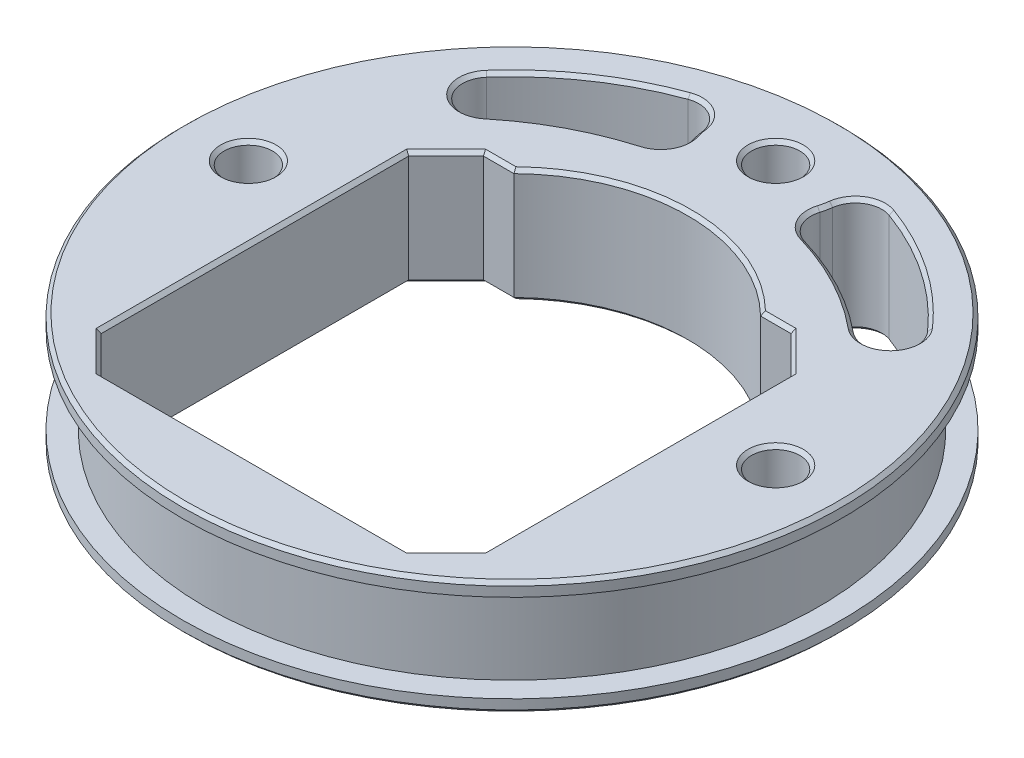
SolidWorks part; units mm, degrees
ref_plane "Front Plane" through (0, 0, 0) normal (0, 0, 1) x (1, 0, 0)
ref_plane "Top Plane" through (0, 0, 0) normal (0, 1, 0) x (1, 0, 0)
ref_plane "Right Plane" through (0, 0, 0) normal (1, 0, 0) x (0, 0, -1)
sketch "Sketch1" plane through (0, 0, 0) normal (0, 1, 0) x (1, 0, 0)
  line L0 (0, 0) -> (0, -7.5) construction
  line L1 (-17.4944, 14.25) -> (-14.0334, 14.25)
  line L2 (17.4944, 14.25) -> (21.75, 9.9944)
  line L3 (21.75, 9.9944) -> (21.75, -24.9944)
  line L4 (21.75, -24.9944) -> (17.4944, -29.25)
  line L5 (17.4944, -29.25) -> (-17.4944, -29.25)
  line L6 (-17.4944, -29.25) -> (-21.75, -24.9944)
  line L7 (-21.75, -24.9944) -> (-21.75, 9.9944)
  line L8 (-21.75, 9.9944) -> (-17.4944, 14.25)
  line L9 (14.0334, 14.25) -> (17.4944, 14.25)
  circle A0 centre (0, 0) radius 35 construction
  circle A1 centre (0, -7.5) radius 27.9127 construction
  circle A2 centre (0, 0) radius 30 construction
  circle A3 centre (0, 30) radius 2.75
  circle A4 centre (30, 0) radius 2.75
  circle A5 centre (-30, 0) radius 2.75
  circle A6 centre (0, 0) radius 37.5
  arc A7 (-20.9311, 17.8995) -> (20.9311, 17.8995) centre (0, -7.5) ccw construction
  arc A8 (7.1823, 27.8402) -> (7.4393, 29.0476) centre (0, 30) ccw
  arc A9 (6.9711, 32.7667) -> (-6.9711, 32.7667) centre (0, 0) ccw construction
  arc A10 (-25.0854, 22.203) -> (-20.9311, 17.8995) centre (-22.8389, 20.2147) ccw
  arc A11 (20.9311, 17.8995) -> (25.0854, 22.203) centre (22.8389, 20.2147) ccw
  arc A12 (-5.5389, 24.9433) -> (5.5389, 24.9433) centre (0, 30) ccw construction
  arc A13 (5.5389, 24.9433) -> (-5.5389, 24.9433) centre (0, -7.5) ccw construction
  arc A14 (-9.2152, 24.0963) -> (-20.9311, 17.8995) centre (0, -7.5) ccw
  arc A15 (20.9311, 17.8995) -> (9.2152, 24.0963) centre (0, -7.5) ccw
  arc A16 (25.0854, 22.203) -> (11.4394, 31.4863) centre (0, 0) ccw
  arc A17 (-11.4394, 31.4863) -> (-25.0854, 22.203) centre (0, 0) ccw
  arc A18 (-25.0854, 22.203) -> (25.0854, 22.203) centre (0, 0) ccw construction
  arc A19 (-7.4393, 29.0476) -> (-7.1823, 27.8402) centre (0, 30) ccw
  arc A20 (6.9711, 32.7667) -> (-6.9711, 32.7667) centre (0, 30) ccw construction
  arc A21 (11.4394, 31.4863) -> (7.4393, 29.0476) centre (10.415, 28.6667) ccw
  arc A22 (7.1823, 27.8402) -> (9.2152, 24.0963) centre (10.0552, 26.9763) ccw
  arc A23 (-9.2152, 24.0963) -> (-7.1823, 27.8402) centre (-10.0552, 26.9763) ccw
  arc A24 (-11.4394, 31.4863) -> (-7.4393, 29.0476) centre (-10.415, 28.6667) cw
  arc A25 (14.0334, 14.25) -> (-14.0334, 14.25) centre (0, 0) ccw
  dimension "D1" = 43.5
  dimension "D2" = 70
  dimension "D5" = 60
  dimension "D6" = 5.5
  dimension "D7" = 2.5
  dimension "D8" = 4
  dimension "D9" = 5
  dimension "D10" = 3
  dimension "D11" = 3
  dimension "D12" = 20
  dimension "D3" = 7.5
  dimension "D4" = 55.5
extrude "Boss-Extrude1" add sketch "Sketch1" along normal mid plane 13
sketch "Sketch2" plane through (0, 0, 0) normal (0, 1, 0) x (1, 0, 0)
  circle A0 centre (0, 0) radius 34.9
  dimension "D1" = 69.8
extrude "Cut-Extrude-Thin1" cut sketch "Sketch2" against normal mid plane 10 thin
chamfer "Chamfer1" distance 0.4 angle 45 2 edges at (0, -6.5, 37.5) (0, 6.5, 37.5)
chamfer "Chamfer2" distance 0.4 angle 45 50 edges at (-15.7639, -6.5, -14.25) (0, -6.5, -20) (15.7639, -6.5, -14.25) (19.6222, -6.5, -12.1222) (21.75, -6.5, 7.5) (19.6222, -6.5, 27.1222) (0, -6.5, 29.25) (-19.6222, -6.5, 27.1222) (-21.75, -6.5, 7.5) (-19.6222, -6.5, -12.1222) (30, -6.5, 2.75) (30, 6.5, 2.75) (-30, -6.5, 2.75) (-30, 6.5, 2.75) (0, -6.5, -27.25) (0, 6.5, -27.25) (-15.3883, 6.5, -21.5937) (-7.4188, 6.5, -25.5447) (-24.9973, 6.5, -18.1311) (-7.3357, 6.5, -28.4386) (-18.843, 6.5, -27.6982) (-8.8534, 6.5, -31.2282) (-15.3883, -6.5, -21.5937) (-7.4188, -6.5, -25.5447) (-24.9973, -6.5, -18.1311) (-7.3357, -6.5, -28.4386) (-18.843, -6.5, -27.6982) (-8.8534, -6.5, -31.2282) (7.4188, 6.5, -25.5447) (15.3883, 6.5, -21.5937) (7.3357, 6.5, -28.4386) (24.9973, 6.5, -18.1311) (8.8534, 6.5, -31.2282) (18.843, 6.5, -27.6982) (7.4188, -6.5, -25.5447) (15.3883, -6.5, -21.5937) (7.3357, -6.5, -28.4386) (24.9973, -6.5, -18.1311) (8.8534, -6.5, -31.2282) (18.843, -6.5, -27.6982) (15.7639, 6.5, -14.25) (19.6222, 6.5, -12.1222) (21.75, 6.5, 7.5) (19.6222, 6.5, 27.1222) (0, 6.5, 29.25) (-19.6222, 6.5, 27.1222) (-21.75, 6.5, 7.5) (-19.6222, 6.5, -12.1222) (0, 6.5, -20) (-15.7639, 6.5, -14.25)
